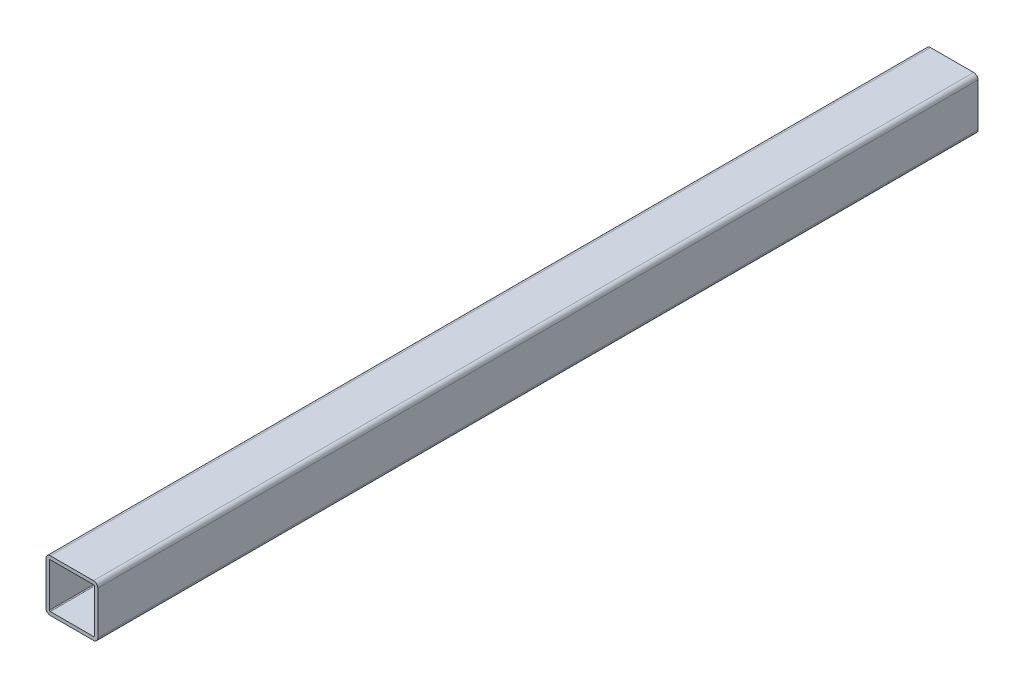
SolidWorks part; units mm, degrees
ref_plane "Front Plane" through (0, 0, 0) normal (0, 0, 1) x (1, 0, 0)
ref_plane "Top Plane" through (0, 0, 0) normal (0, 1, 0) x (1, 0, 0)
ref_plane "Right Plane" through (0, 0, 0) normal (1, 0, 0) x (0, 0, -1)
sketch "Sketch1" plane through (0, 0, 0) normal (0, 0, 1) x (1, 0, 0)
  line L1 (-15.875, 19.05) -> (15.875, 19.05)
  line L2 (-19.05, 15.875) -> (-19.05, -15.875)
  line L3 (-15.875, -19.05) -> (15.875, -19.05)
  line L4 (19.05, 15.875) -> (19.05, -15.875)
  line L5 (-19.05, 19.05) -> (19.05, -19.05) construction
  line L6 (-19.05, -19.05) -> (19.05, 19.05) construction
  arc A0 (-19.05, -15.875) -> (-15.875, -19.05) centre (-15.875, -15.875) ccw
  arc A1 (15.875, -19.05) -> (19.05, -15.875) centre (15.875, -15.875) ccw
  arc A2 (19.05, 15.875) -> (15.875, 19.05) centre (15.875, 15.875) ccw
  arc A3 (-15.875, 19.05) -> (-19.05, 15.875) centre (-15.875, 15.875) ccw
  point P0 (0, 0)
  dimension "D3" = 3.175
  dimension "D1" = 38.1
  dimension "D2" = 38.1
extrude "Extrude-Thin1" add sketch "Sketch1" along normal mid plane 647.7 thin
sketch "Sketch3" plane through (19.05, 0, 0) normal (1, 0, 0) x (0, 0, -1)
  line L0 (323.85, 0) -> (-323.85, 0) construction
  line L1 (323.85, -15.875) -> (323.85, 15.875) construction
  line L2 (-323.85, -15.875) -> (-323.85, 15.875) construction
  line L3 (304.8, 19.05) -> (304.8, -19.05) construction
  line L4 (-323.85, 19.05) -> (323.85, 19.05) construction
  line L5 (-323.85, -19.05) -> (323.85, -19.05) construction
  line L6 (-304.8, 19.05) -> (-304.8, -19.05) construction
  line L7 (-228.6, 19.05) -> (-228.6, -19.05) construction
  line L8 (-152.4, 19.05) -> (-152.4, -19.05) construction
  line L9 (-76.2, 19.05) -> (-76.2, -19.05) construction
  dimension "D1" = 19.05
  dimension "D2" = 19.05
  dimension "D3" = 76.2
  dimension "D4" = 76.2
  dimension "D5" = 76.2
